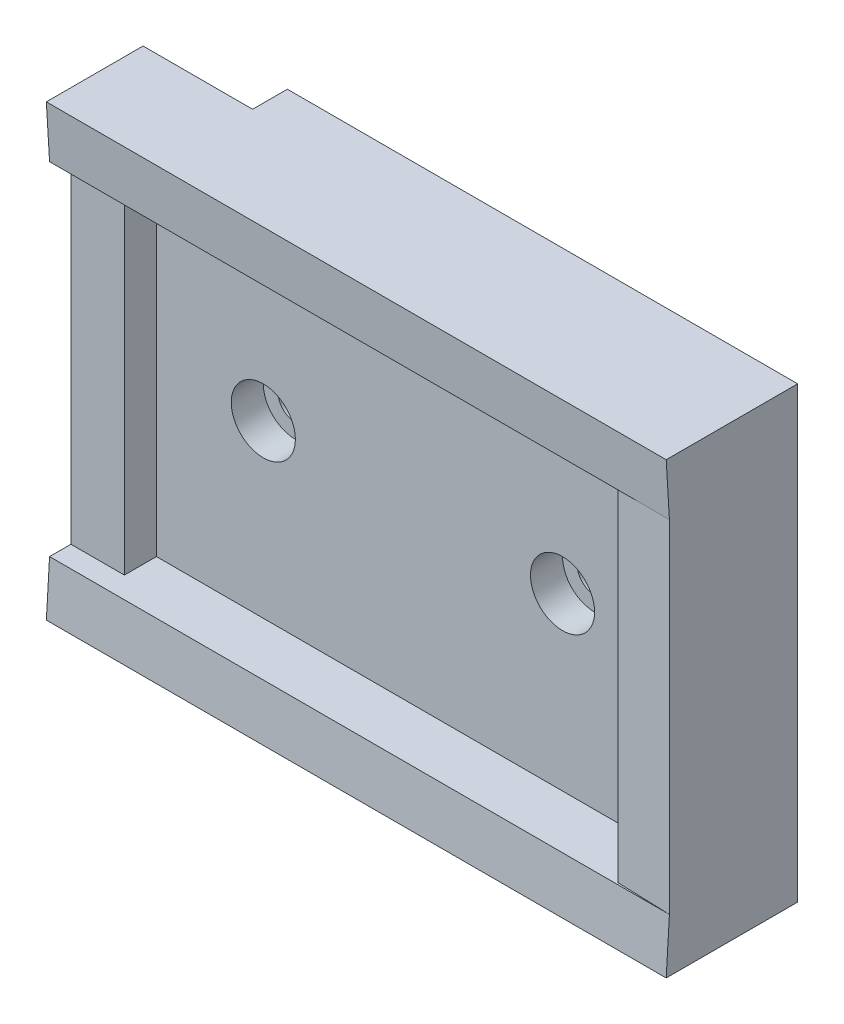
SolidWorks part; units mm, degrees
ref_plane "Plan de face" through (0, 0, 0) normal (0, 0, 1) x (1, 0, 0)
ref_plane "Plan de dessus" through (0, 0, 0) normal (0, 1, 0) x (1, 0, 0)
ref_plane "Plan de droite" through (0, 0, 0) normal (1, 0, 0) x (0, 0, -1)
sketch "Esquisse1" plane through (0, 0, 0) normal (0, 0, 1) x (1, 0, 0)
  line L1 (0, 0) -> (58, 0)
  line L2 (0, 0) -> (0, -32)
  line L3 (0, -32) -> (58, -32)
  line L4 (58, 0) -> (58, -32)
  dimension "D1" = 58
  dimension "D2" = 32
extrude "Boss.-Extru.1" add sketch "Esquisse1" along normal blind 7
sketch "Esquisse2" plane through (0, 0, 7) normal (0, 0, 1) x (1, 0, 0)
  line L0 (0, -32) -> (58, -32) construction
  line L1 (0, 0) -> (5, 0)
  line L2 (0, 0) -> (0, -32)
  line L3 (0, -32) -> (5, -32)
  line L4 (5, 0) -> (5, -32)
  dimension "D1" = 5
extrude "Boss.-Extru.3" add sketch "Esquisse2" along normal blind 3
sketch "Esquisse3" plane through (0, 0, 7) normal (0, 0, 1) x (1, 0, 0)
  line L0 (5, -32) -> (58, -32) construction
  line L1 (58, 0) -> (53, 0)
  line L2 (58, 0) -> (58, -32)
  line L3 (58, -32) -> (53, -32)
  line L4 (53, 0) -> (53, -32)
  dimension "D1" = 5
extrude "Boss.-Extru.4" add sketch "Esquisse3" along normal blind 5
sketch "Esquisse4" plane through (0, -32, 0) normal (0, -1, 0) x (1, 0, 0)
  line L0 (0, 10) -> (58, 12)
  line L1 (58, 12) -> (0, 12)
  line L2 (0, 12) -> (0, 10)
  line L3 (0, 10) -> (5, 10) construction
  line L4 (5, 10) -> (5, 7) construction
  point P6 (0, 11)
  dimension "D1" = 0
  dimension "D2" = 5
extrude "Enlèv. mat.-Extru.1" cut sketch "Esquisse4" against normal through all
sketch "Esquisse6" plane through (0, 0, 7) normal (0, 0, 1) x (1, 0, 0)
  line L0 (5, -32) -> (5, 0) construction
  line L1 (58, -32) -> (58, 0) construction
  line L2 (0, 0) -> (0, -32) construction
  circle A0 centre (43, -16) radius 1.625
  circle A1 centre (15, -16) radius 1.625
  point P11 (5, -16)
  dimension "D1" = 3.25
  dimension "D2" = 3.25
  dimension "D3" = 15
  dimension "D4" = 15
extrude "Enlèv. mat.-Extru.2" cut sketch "Esquisse6" against normal through all
sketch "Esquisse8" plane through (0, 0, 7) normal (0, 0, 1) x (1, 0, 0)
  circle A0 centre (15, -16) radius 3
  circle A1 centre (43, -16) radius 3
  dimension "D1" = 6
  dimension "D2" = 6
extrude "Enlèv. mat.-Extru.4" cut sketch "Esquisse8" against normal blind 3
sketch "Esquisse7" plane through (0, -32, 0) normal (0, -1, 0) x (1, 0, 0)
  line L1 (0, 0) -> (10.25, 0)
  line L2 (0, 0) -> (0, 3.25)
  line L3 (0, 3.25) -> (10.25, 3.25)
  line L4 (10.25, 0) -> (10.25, 3.25)
  dimension "D1" = 10.25
  dimension "D2" = 3.25
extrude "Enlèv. mat.-Extru.3" cut sketch "Esquisse7" against normal blind 50 and the other way blind 10
sketch "Esquisse9" plane through (0, 0, 0) normal (0, 0, 1) x (1, 0, 0)
  line L0 (0, 0) -> (0, -32) construction
  line L1 (58, 0) -> (0, 0)
  line L2 (58, 0) -> (58, 5)
  line L3 (58, 5) -> (0, 5)
  line L4 (0, 0) -> (0, 5)
  line L5 (58, -32) -> (0, -32)
  line L6 (58, -32) -> (58, -37)
  line L7 (58, -37) -> (0, -37)
  line L8 (0, -32) -> (0, -37)
  dimension "D1" = 5
  dimension "D2" = 5
extrude "Boss.-Extru.5" add sketch "Esquisse9" along normal blind 12
sketch "Esquisse10" plane through (0, 0, 0) normal (-1, 0, 0) x (0, 0, 1)
  line L0 (12, 5) -> (12.3, 5)
  line L1 (12.3, 5) -> (12, 0)
  line L2 (12, 0) -> (12, 5)
  line L3 (12, -32) -> (12, -37)
  line L4 (12, -37) -> (12.3, -37)
  line L5 (12.3, -37) -> (12, -32)
  dimension "D1" = 0.3
  dimension "D2" = 0.3
extrude "Boss.-Extru.6" add sketch "Esquisse10" against normal through all
sketch "Esquisse12" plane through (0, 0, 0) normal (0, 0, -1) x (-1, 0, 0)
  line L0 (-10.25, 0) -> (-10.25, 5)
  line L1 (-58, 5) -> (0, 5) construction
  line L2 (-10.25, -32) -> (-10.25, -37)
  line L3 (0, -37) -> (-58, -37) construction
  line M4 (-10.25, 0) -> (0, 0)
  line M5 (0, 0) -> (0, 5)
  line M6 (0, 5) -> (-58, 5)
  line M8 (-58, -37) -> (0, -37)
  line M9 (0, -37) -> (0, -32)
  line M10 (0, -32) -> (-10.25, -32)
extrude "Enlèv. mat.-Extru.5" cut sketch "Esquisse12" against normal blind 3.25 contours L2 M10 M8 M9 | L0 M4 M5 M6
